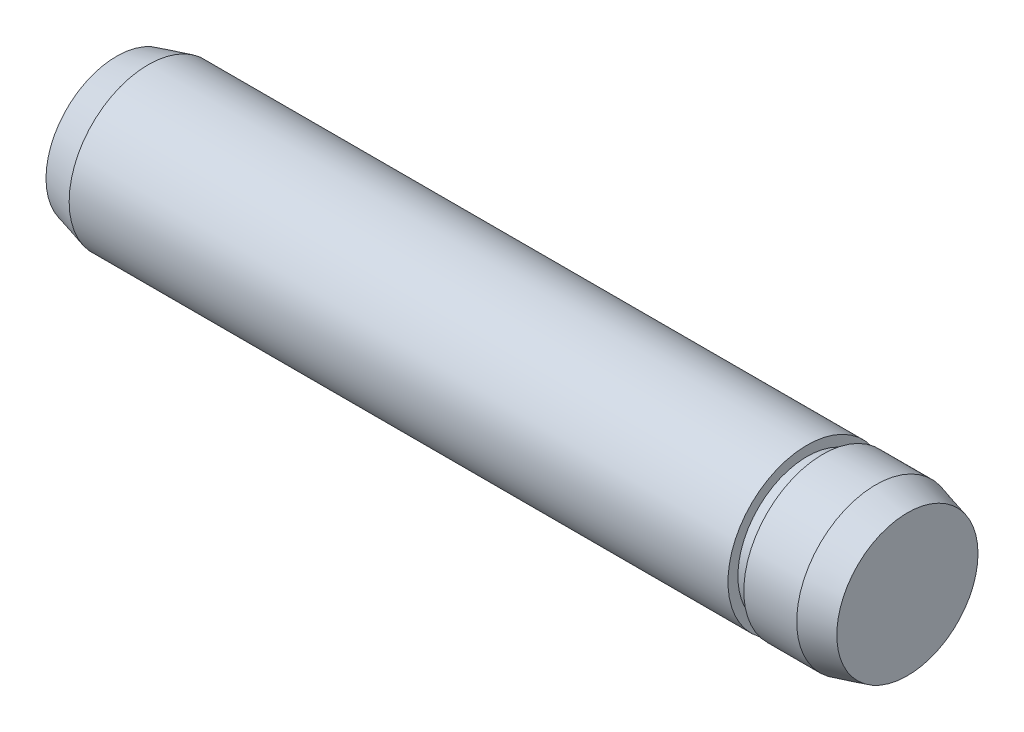
SolidWorks part; units mm, degrees
ref_plane "Front Plane" through (0, 0, 0) normal (0, 0, 1) x (1, 0, 0)
ref_plane "Top Plane" through (0, 0, 0) normal (0, 1, 0) x (1, 0, 0)
ref_plane "Right Plane" through (0, 0, 0) normal (1, 0, 0) x (0, 0, -1)
sketch "Sketch1" plane through (0, 0, 0) normal (0, 0, 1) x (1, 0, 0)
  line L0 (-18.4, 0) -> (18.4, 0) construction
  line L1 (18.4, 4) -> (18.4, -4) construction
  line L2 (-18.4, 4) -> (-18.4, -4) construction
  line L3 (20, 4) -> (20, -4) construction
  line L4 (-20, 4) -> (-20, -4) construction
  line L5 (-18.4, 0) -> (-20, 0) construction
  line L6 (18.4, 0) -> (20, 0) construction
  dimension "Dia" = 8
  dimension "C" = 1.6
  dimension "D1" = 1.6
  dimension "Length" = 40
sketch "Sketch2" plane through (0, 0, 0) normal (1, 0, 0) x (0, 0, -1)
  circle A0 centre (0, 0) radius 4
extrude "Extrude1" add sketch "Sketch2" against normal up to vertex (18.4 mm away) and the other way up to vertex (18.4 mm away) up to point (-18.4, 4, 0) other way up to point (18.4, 4, 0)
sketch "Sketch3" plane through (18.4, 0, 0) normal (1, 0, 0) x (0, 0, -1)
  circle A1 centre (0, 0) radius 4
  circle A2 centre (0, 0) radius 4
  dimension "D1" = 0
extrude "Extrude2" add sketch "Sketch3" along normal up to vertex (1.6 mm away) draft 15 up to point (20, 0, 0)
sketch "Sketch4" plane through (-18.4, 0, 0) normal (-1, 0, 0) x (0, 0, 1)
  circle A1 centre (0, 0) radius 4
  circle A2 centre (0, 0) radius 4
  dimension "D1" = 0
extrude "Extrude3" add sketch "Sketch4" along normal up to vertex (1.6 mm away) draft 15 up to point (-20, 0, 0)
ref_plane "Plane1" through (14.925, 0, 0) normal (1, 0, 0) x (0, 0, -1)
sketch "Sketch5" plane through (14.925, 0, 0) normal (1, 0, 0) x (0, 0, -1)
  circle A0 centre (0, 0) radius 4
  circle A1 centre (0, 0) radius 3.5
  dimension "D1" = 7
extrude "Cut-Extrude1" cut sketch "Sketch5" along normal blind 0.8
equation "\"D1@Sketch1\" = \"C@Sketch1\""
